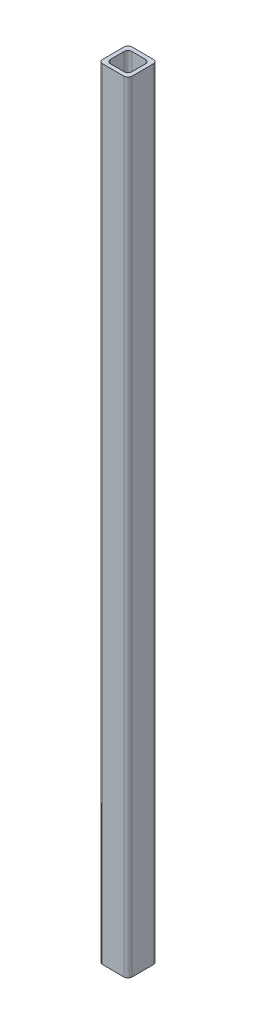
SolidWorks part; units mm, degrees
ref_plane "Front Plane" through (0, 0, 0) normal (0, 0, 1) x (1, 0, 0)
ref_plane "Top Plane" through (0, 0, 0) normal (0, 1, 0) x (1, 0, 0)
ref_plane "Right Plane" through (0, 0, 0) normal (1, 0, 0) x (0, 0, -1)
sketch "Sketch1" plane through (0, 0, 0) normal (0, 1, 0) x (1, 0, 0)
  line L1 (11, 15) -> (-11, 15)
  line L2 (15, 11) -> (15, -11)
  line L3 (11, -15) -> (-11, -15)
  line L4 (-15, 11) -> (-15, -11)
  line L5 (7, 11) -> (-7, 11)
  line L6 (11, 7) -> (11, -7)
  line L7 (7, -11) -> (-7, -11)
  line L8 (-11, 7) -> (-11, -7)
  line L9 (11, 11) -> (-11, -11) construction
  line L10 (11, -11) -> (-11, 11) construction
  arc A0 (-15, 11) -> (-11, 15) centre (-11, 11) cw
  arc A1 (11, 15) -> (15, 11) centre (11, 11) cw
  arc A2 (15, -11) -> (11, -15) centre (11, -11) cw
  arc A3 (-15, -11) -> (-11, -15) centre (-11, -11) ccw
  arc A4 (7, 11) -> (11, 7) centre (7, 7) cw
  arc A5 (11, -7) -> (7, -11) centre (7, -7) cw
  arc A6 (-7, -11) -> (-11, -7) centre (-7, -7) cw
  arc A7 (-7, 11) -> (-11, 7) centre (-7, 7) ccw
  point P0 (0, 0)
  point P14 (0, 0)
  point P15 (-23.3707, 16.2503)
  dimension "D1" = 4
  dimension "D2" = 4
  dimension "D3" = 4
extrude "Boss-Extrude1" add sketch "Sketch1" along normal blind 800
